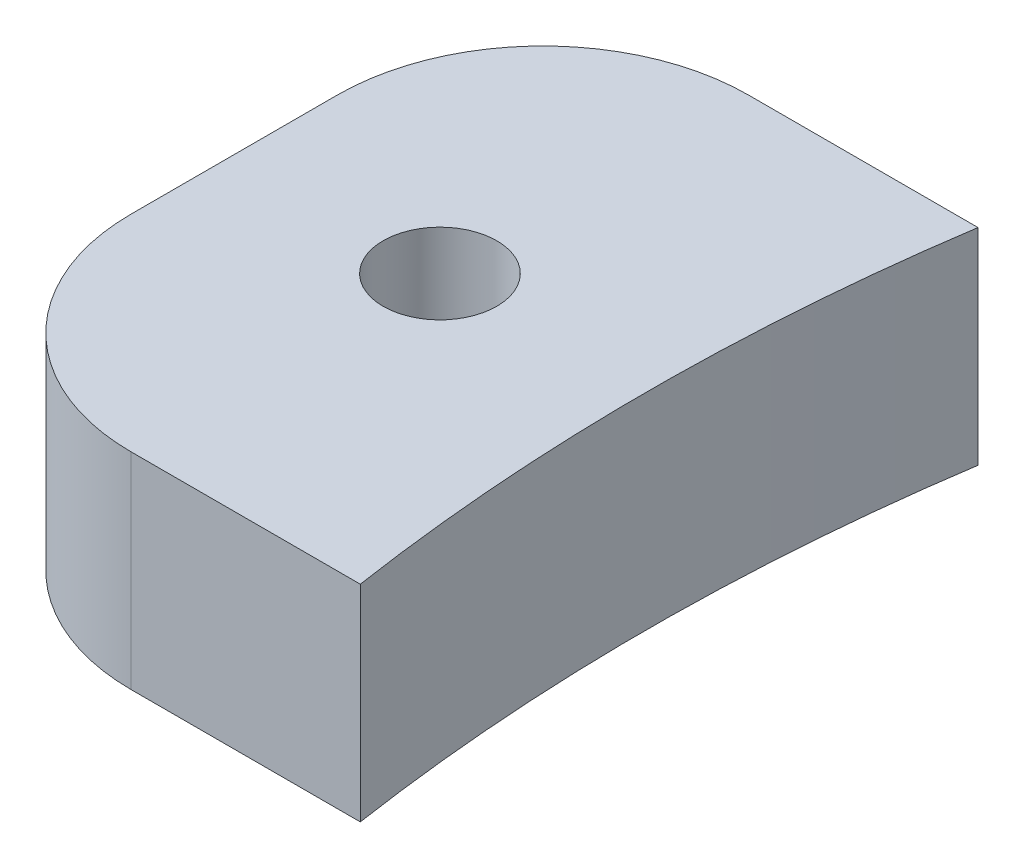
SolidWorks part; units mm, degrees
material "6061 Alloy"
ref_plane "Front Plane" through (0, 0, 0) normal (0, 0, 1) x (1, 0, 0)
ref_plane "Top Plane" through (0, 0, 0) normal (0, 1, 0) x (1, 0, 0)
ref_plane "Right Plane" through (0, 0, 0) normal (1, 0, 0) x (0, 0, -1)
sketch "Sketch1" plane through (0, 0, 0) normal (0, 1, 0) x (1, 0, 0)
  line L1 (-69.85, 9.525) -> (0, 9.525)
  line L2 (-76.2, 3.175) -> (-76.2, -3.175)
  line L3 (-69.85, -9.525) -> (0, -9.525)
  line L4 (0, 9.525) -> (0, -9.525)
  arc A0 (-69.85, 9.525) -> (-76.2, 3.175) centre (-69.85, 3.175) ccw
  arc A1 (-69.85, -9.525) -> (-76.2, -3.175) centre (-69.85, -3.175) cw
  point P7 (-76.2, 9.525)
  point P10 (-76.2, -9.525)
  dimension "D3" = 6.35
  dimension "D1" = 19.05
  dimension "D2" = 76.2
extrude "Extrude1" add sketch "Sketch1" along normal blind 6.35
sketch "Sketch2" plane through (0, 6.35, 0) normal (0, 1, 0) x (-1, 0, 0)
  circle A0 centre (0, 0) radius 63.5
extrude "Cut-Extrude1" cut sketch "Sketch2" against normal blind 6.35
hole_wizard "#6-32 Tapped Hole1" positions "3DSketch1" profile "Sketch3" tap size "#6-32" standard "Ansi Inch"
sketch3d "3DSketch1"
  line L0 (-62.7816, 6.35, -9.525) -> (-69.85, 6.35, -9.525) construction
  line L2 (-76.2, 6.35, -3.175) -> (-76.2, 6.35, 3.175) construction
  point P0 (-69.85, 6.35, 0)
  dimension "D1" = 9.525
  dimension "D2" = 6.35
sketch "Sketch3" plane through (-69.85, 6.35, 0) normal (1, 0, 0) x (0, 0, 1)
  line L0 (0, 0) -> (0, 10.2107)
  line L1 (0, 10.2107) -> (1.3525, 9.398)
  line L2 (1.3525, 9.398) -> (1.3525, 7.112)
  line L3 (1.3525, 7.112) -> (1.7526, 7.112)
  line L4 (1.7526, 7.112) -> (1.7526, 0)
  line L5 (1.7526, 0) -> (0, 0)
  line L10 (0, 10.2107) -> (-1.3526, 9.398) construction
  line L11 (0, -6.35) -> (0, 107.95) construction
  dimension "Tap Drill Dia." = 2.7051
  dimension "Tap Drill Depth" = 9.398
  dimension "Thread Major Dia." = 3.5052
  dimension "Thread Depth" = 7.112
  dimension "Drill Angle" = 118
